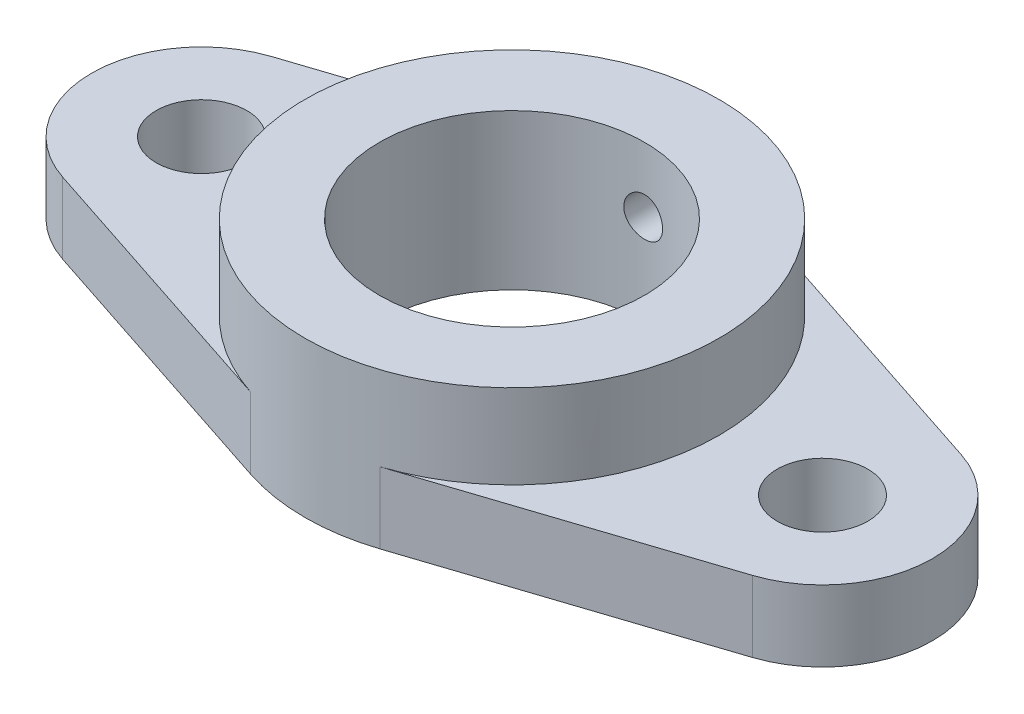
SolidWorks part; units mm, degrees
ref_plane "정면" through (0, 0, 0) normal (0, 0, 1) x (1, 0, 0)
ref_plane "윗면" through (0, 0, 0) normal (0, 1, 0) x (1, 0, 0)
ref_plane "우측면" through (0, 0, 0) normal (1, 0, 0) x (0, 0, -1)
sketch "스케치1" plane through (0, 0, 0) normal (0, 1, 0) x (1, 0, 0)
  line L0 (-53.3125, 16.1486) -> (-10, 30.3974)
  line L1 (10, 30.3974) -> (53.3125, 16.1486)
  line L2 (-53.3125, -16.1486) -> (-10, -30.3974)
  line L3 (10, -30.3974) -> (53.3125, -16.1486)
  arc A0 (10, 30.3974) -> (-10, 30.3974) centre (0, 0) ccw
  arc A1 (53.3125, -16.1486) -> (53.3125, 16.1486) centre (48, 0) ccw
  arc A4 (-10, -30.3974) -> (10, -30.3974) centre (0, 0) ccw
  arc A6 (-53.3125, 16.1486) -> (-53.3125, -16.1486) centre (-48, 0) ccw
  point P7 (0, 0)
  point P8 (0, 0)
  point P11 (0, 0)
  point P12 (5.541, 31.8643)
  dimension "D1" = 64
  dimension "D2" = 17
  dimension "D3" = 34
  dimension "D7" = 0
  dimension "D4" = 48
  dimension "D5" = 48
  dimension "D6" = 0
extrude "보스-돌출2" add sketch "스케치1" along normal blind 11 contours L2 A4 L3 A1 L1 A0 L0 A6
sketch "스케치2" plane through (0, 0, 0) normal (0, 1, 0) x (1, 0, 0)
  circle A0 centre (-48, 0) radius 7
  circle A1 centre (48, 0) radius 7
  arc A2 (-53.3125, 16.1486) -> (-53.3125, -16.1486) centre (-48, 0) ccw construction
  arc A3 (53.3125, -16.1486) -> (53.3125, 16.1486) centre (48, 0) ccw construction
  dimension "D1" = 14
  dimension "D2" = 14
extrude "컷-돌출1" cut sketch "스케치2" along normal blind 11
sketch "스케치3" plane through (0, 0, 0) normal (0, 1, 0) x (1, 0, 0)
  circle A0 centre (0, 0) radius 32
  arc A1 (-10, -30.3974) -> (10, -30.3974) centre (0, 0) ccw construction
extrude "보스-돌출3" add sketch "스케치3" along normal blind 24
sketch "스케치4" plane through (0, 0, 0) normal (0, 1, 0) x (1, 0, 0)
  circle A0 centre (0, 0) radius 20.5
  dimension "D1" = 41
extrude "컷-돌출2" cut sketch "스케치4" along normal through all
sketch "스케치5" plane through (0, 0, 0) normal (0, 0, 1) x (1, 0, 0)
  line L2 (10, 11) -> (53.3125, 11) construction
  circle A0 centre (0, 14) radius 3
  point P2 (0, 0)
  point P3 (0, 15.4376)
  point P4 (0, 0)
  dimension "D1" = 6
extrude "컷-돌출3" cut sketch "스케치5" against normal through all
